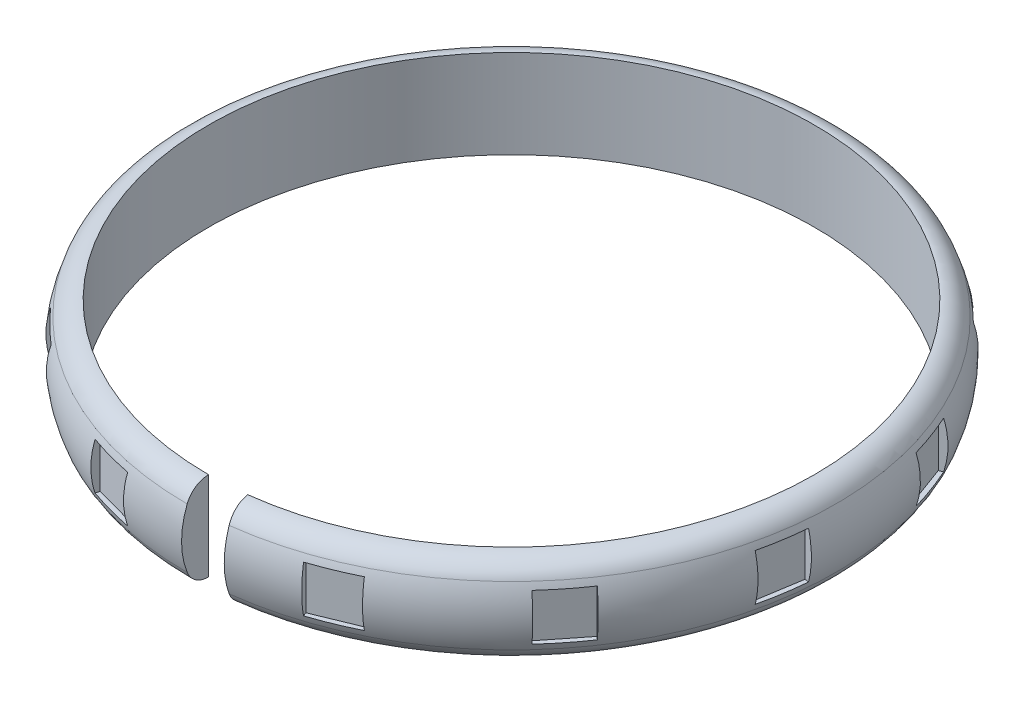
SolidWorks part; units mm, degrees
material "Лист Д16А.Т хх ГОСТ 21631-76"
ref_plane "Front" through (0, 0, 0) normal (0, 0, 1) x (1, 0, 0)
ref_plane "Top" through (0, 0, 0) normal (0, 1, 0) x (1, 0, 0)
ref_plane "Right" through (0, 0, 0) normal (1, 0, 0) x (0, 0, -1)
sketch "Эскиз1" plane through (0, 0, 0) normal (1, 0, 0) x (0, 0, -1)
  line L0 (0, 39.7057) -> (0, 0) construction
  line L1 (-32.5, -4.75) -> (-32.5, 4.75)
  line L2 (-35.4, 0) -> (-32.5, 0) construction
  line L3 (-32.5, 4.75) -> (-35.8253, 4.75) construction
  arc A0 (-32.5, 4.75) -> (-34.8, 3.1801) centre (-32.5, 2.2802) ccw
  arc A1 (-34.8, 3.1801) -> (-35.4, 0) centre (-26.6723, 0) ccw
  arc A2 (-34.8, -3.1801) -> (-35.4, 0) centre (-26.6723, 0) cw
  arc A3 (-32.5, -4.75) -> (-34.8, -3.1801) centre (-32.5, -2.2802) cw
  point P9 (-56.3018, 3.3175)
  point P14 (-55.8977, 3.1801)
  dimension "D1" = 2.9
  dimension "D2" = 9.5
  dimension "D3" = 2.3
  dimension "D4" = 6.3603
  dimension "D5" = 65
revolve "Повернуть1" add sketch "Эскиз1" angle 353 about L0
sketch "Эскиз2" plane through (0, 0, 0) normal (0, 1, 0) x (1, 0, 0)
  line L0 (-11.5225, -32.6149) -> (-6.7, -33.9354)
  line L1 (-11.5225, -32.6149) -> (-12.3148, -35.5084)
  line L2 (-6.7, -33.9354) -> (-7.4923, -36.8289)
  line L3 (-12.3148, -35.5084) -> (-7.4923, -36.8289)
  line L4 (-11.5225, -32.6149) -> (-7.4923, -36.8289) construction
  line L5 (-6.7, -33.9354) -> (-12.3148, -35.5084) construction
  line L6 (-9.5074, -34.7219) -> (0, 0) construction
  line L7 (-22.4528, -26.313) -> (-24.5599, -28.4484)
  line L8 (-26.0117, -22.8011) -> (-22.4528, -26.313)
  line L9 (-26.0117, -22.8011) -> (-28.1189, -24.9365)
  line L10 (-28.1189, -24.9365) -> (-24.5599, -28.4484)
  line L11 (-32.4586, -11.9557) -> (-35.3413, -12.7864)
  line L12 (-33.8432, -7.1512) -> (-32.4586, -11.9557)
  line L13 (-33.8432, -7.1512) -> (-36.7259, -7.9819)
  line L14 (-36.7259, -7.9819) -> (-35.3413, -12.7864)
  line L15 (-34.1565, 5.4618) -> (-37.0769, 6.1483)
  line L16 (-33.0123, 10.3291) -> (-34.1565, 5.4618)
  line L17 (-33.0123, 10.3291) -> (-35.9327, 11.0156)
  line L18 (-35.9327, 11.0156) -> (-37.0769, 6.1483)
  line L19 (-27.1119, 21.4812) -> (-29.3225, 23.5094)
  line L20 (-23.7317, 25.1656) -> (-27.1119, 21.4812)
  line L21 (-23.7317, 25.1656) -> (-25.9423, 27.1937)
  line L22 (-25.9423, 27.1937) -> (-29.3225, 23.5094)
  line L23 (-13.1279, 32.0025) -> (-14.0629, 34.8531)
  line L24 (-8.3769, 33.5608) -> (-13.1279, 32.0025)
  line L25 (-8.3769, 33.5608) -> (-9.3119, 36.4114)
  line L26 (-9.3119, 36.4114) -> (-14.0629, 34.8531)
  line L27 (4.2163, 34.3325) -> (4.7962, 37.2759)
  line L28 (9.122, 33.366) -> (4.2163, 34.3325)
  line L29 (9.122, 33.366) -> (9.7019, 36.3094)
  line L30 (9.7019, 36.3094) -> (4.7962, 37.2759)
  line L31 (20.4813, 27.875) -> (22.4277, 30.1579)
  line L32 (24.2861, 24.631) -> (20.4813, 27.875)
  line L33 (24.2861, 24.631) -> (26.2325, 26.9139)
  line L34 (26.2325, 26.9139) -> (22.4277, 30.1579)
  line L35 (31.504, 14.2827) -> (34.3187, 15.3208)
  line L36 (33.234, 9.5916) -> (31.504, 14.2827)
  line L37 (33.234, 9.5916) -> (36.0487, 10.6296)
  line L38 (36.0487, 10.6296) -> (34.3187, 15.3208)
  line L39 (34.4631, -2.9653) -> (37.4257, -3.4378)
  line L40 (33.6756, -7.9029) -> (34.4631, -2.9653)
  line L41 (33.6756, -7.9029) -> (36.6381, -8.3754)
  line L42 (36.6381, -8.3754) -> (37.4257, -3.4378)
  line L43 (28.6012, -19.4543) -> (30.9534, -21.3164)
  line L44 (25.4977, -23.3745) -> (28.6012, -19.4543)
  line L45 (25.4977, -23.3745) -> (27.8498, -25.2366)
  line L46 (27.8498, -25.2366) -> (30.9534, -21.3164)
  line L47 (15.4187, -30.9639) -> (16.5584, -33.739)
  line L48 (10.7935, -32.8633) -> (15.4187, -30.9639)
  line L49 (10.7935, -32.8633) -> (11.9332, -35.6384)
  line L50 (11.9332, -35.6384) -> (16.5584, -33.739)
  line L63 (0, -34.8) -> (0, -32.5) construction
  arc A0 (3.9608, -32.2577) -> (0, -32.5) centre (0, 0) ccw construction
  point P1 (-9.5074, -34.7219)
  point P3 (-8.5831, -31.3462)
  point P14 (0, 0)
  point P15 (0, 0)
  point P70 (0, 0)
  point P71 (11.5636, -32.6004)
  point P72 (5.5851, -34.3756)
  dimension "D1" = 5
  dimension "D2" = 2
  dimension "D3" = 3
  dimension "D5" = 6.7
  dimension "D6" = 17.5
  dimension "D4" = 12
extrude "Вырез-Вытянуть1" cut sketch "Эскиз2" against normal mid plane 5
